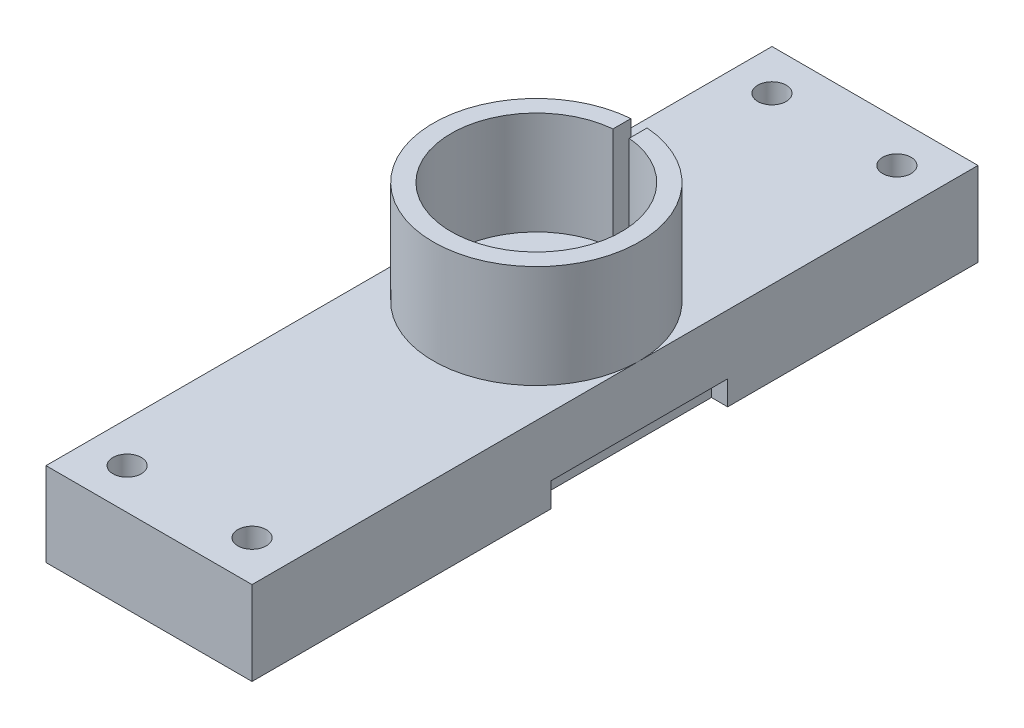
SolidWorks part; units mm, degrees
ref_plane "Front Plane" through (0, 0, 0) normal (0, 0, 1) x (1, 0, 0)
ref_plane "Top Plane" through (0, 0, 0) normal (0, 1, 0) x (1, 0, 0)
ref_plane "Right Plane" through (0, 0, 0) normal (1, 0, 0) x (0, 0, -1)
sketch "Sketch1" plane through (0, 0, 0) normal (0, 1, 0) x (1, 0, 0)
  line L1 (0, 0) -> (25.4, 0)
  line L2 (0, 0) -> (0, 89.5)
  line L3 (0, 89.5) -> (25.4, 89.5)
  line L4 (25.4, 0) -> (25.4, 89.5)
  circle A0 centre (5, 84.5) radius 1.75
  circle A1 centre (20.4, 84.5) radius 1.75
  circle A2 centre (5, 5) radius 1.75
  circle A3 centre (20.4, 5) radius 1.75
  dimension "D3" = 3.5
  dimension "D1" = 89.5
  dimension "D2" = 25.4
  dimension "D4" = 5
  dimension "D5" = 5
  dimension "D6" = 5
  dimension "D7" = 5
extrude "Boss-Extrude1" add sketch "Sketch1" along normal blind 10.35
sketch "Sketch2" plane through (0, 10.35, 0) normal (0, 1, 0) x (1, 0, 0)
  line L1 (25.4, 89.5) -> (0, 89.5) construction
  circle A0 centre (12.7, 47.75) radius 12.7
  circle A1 centre (12.7, 47.75) radius 10.5
  point P2 (12.7, 89.5)
  dimension "D1" = 41.75
  dimension "D2" = 25.4
  dimension "D3" = 21
extrude "Boss-Extrude2" add sketch "Sketch2" along normal blind 12.7
ref_plane "Plane1" through (0, 0, -35.05) normal (0, 0, 1) x (0, -1, 0)
sketch "Sketch5" plane through (0, 23.05, 0) normal (0, 1, 0) x (1, 0, 0)
  line L1 (11.7, 62.7043) -> (13.7, 62.7043)
  line L2 (11.7, 62.7043) -> (11.7, 54.6968)
  line L3 (11.7, 54.6968) -> (13.7, 54.6968)
  line L4 (13.7, 62.7043) -> (13.7, 54.6968)
  circle A0 centre (12.7, 47.75) radius 10.5 construction
  dimension "D1" = 1
  dimension "D2" = 2
extrude "Cut-Extrude1" cut sketch "Sketch5" against normal up to surface (12.7 mm away) up to face at (12.7, 10.35, -71.8)
sketch "Sketch6" plane through (0, 10.35, 0) normal (0, 1, 0) x (1, 0, 0)
  circle A0 centre (12.7, 47.75) radius 6
  dimension "D1" = 12
extrude "Cut-Extrude2" cut sketch "Sketch6" against normal blind 3
sketch "Sketch7" plane through (0, 7.35, 0) normal (0, 1, 0) x (1, 0, 0)
  circle A0 centre (12.7, 47.75) radius 2
  dimension "D1" = 4
extrude "Cut-Extrude3" cut sketch "Sketch7" against normal up to surface (7.35 mm away) up to face at (5, 0, -3.25)
sketch "Sketch8" plane through (25.4, 0, 0) normal (1, 0, 0) x (0, 0, -1)
  line L0 (0, 0) -> (89.5, 0) construction
  line L1 (36.86, 0) -> (58.64, 0)
  line L2 (36.86, 0) -> (36.86, 3)
  line L3 (36.86, 3) -> (58.64, 3)
  line L4 (58.64, 0) -> (58.64, 3)
  line L5 (0, 10.35) -> (0, 0) construction
  line L6 (89.5, 10.35) -> (89.5, 0) construction
  dimension "D1" = 36.86
  dimension "D2" = 30.86
  dimension "D3" = 3
extrude "Cut-Extrude4" cut sketch "Sketch8" against normal blind 2
ref_plane "Plane2" through (12.7, 0, 0) normal (-1, 0, 0) x (0, 0, 1)
mirror "Mirror1" about plane through (12.7, 0, 0) normal (-1, 0, 0) of "Cut-Extrude4"
